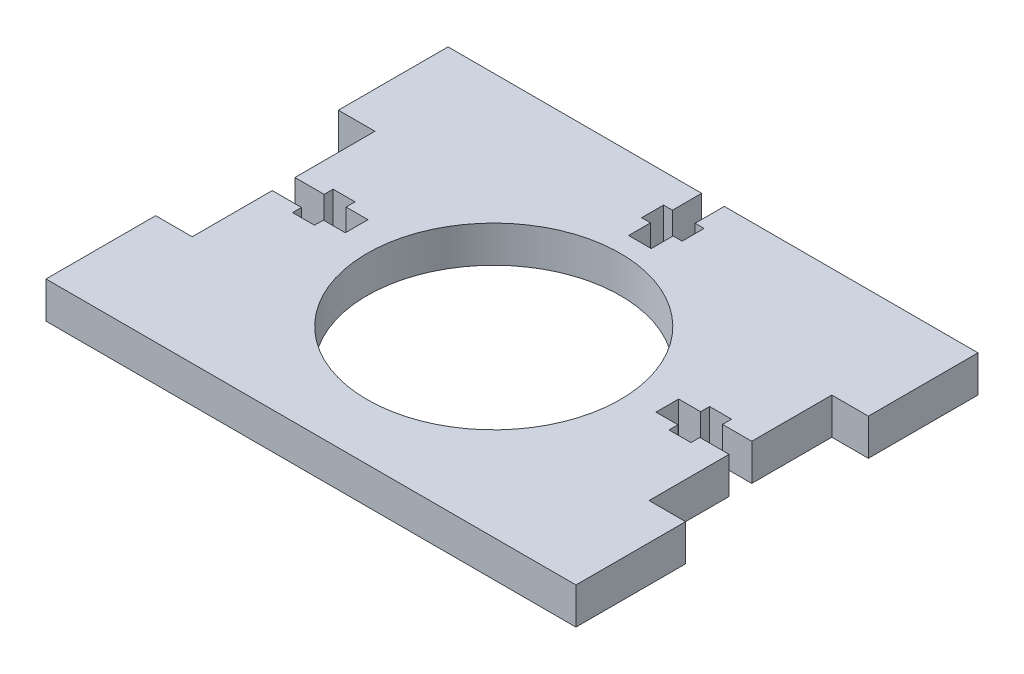
SolidWorks part; units mm, degrees
ref_plane "Plan de face" through (0, 0, 0) normal (0, 0, 1) x (1, 0, 0)
ref_plane "Plan de dessus" through (0, 0, 0) normal (0, 1, 0) x (1, 0, 0)
ref_plane "Plan de droite" through (0, 0, 0) normal (1, 0, 0) x (0, 0, -1)
ref_plane "Plan1" through (0, 5, 0) normal (0, 1, 0) x (1, 0, 0)
sketch "Esquisse1" plane through (0, 5, 0) normal (0, 1, 0) x (1, 0, 0)
  line L0 (31.25, -27.5) -> (31.25, 27.5)
  line L1 (31.25, 27.5) -> (5, 27.5)
  line L2 (5, 27.5) -> (5, -27.5)
  line L3 (5, -27.5) -> (31.25, -27.5)
extrude "Boss.-Extru.1" add sketch "Esquisse1" against normal blind 5
sketch "Esquisse2" plane through (31.25, 0, 0) normal (1, 0, 0) x (0, 0, -1)
  line L0 (27.5, 5) -> (27.5, 0)
  line L1 (27.5, 0) -> (15.45, 0)
  line L2 (15.45, 0) -> (12.5, 2.95)
  line L3 (12.5, 2.95) -> (12.5, 5)
  line L4 (12.5, 5) -> (27.5, 5)
extrude "Boss.-Extru.2" add sketch "Esquisse2" along normal blind 5
sketch "Esquisse3" plane through (31.25, 0, 0) normal (1, 0, 0) x (0, 0, -1)
  line L0 (-15.45, 0) -> (-27.5, 0)
  line L1 (-27.5, 0) -> (-27.5, 5)
  line L2 (-27.5, 5) -> (-12.5, 5)
  line L3 (-12.5, 5) -> (-12.5, 2.95)
  line L4 (-12.5, 2.95) -> (-15.45, 0)
extrude "Boss.-Extru.3" add sketch "Esquisse3" along normal blind 5
sketch "Esquisse4" plane through (0, 0, -27.5) normal (0, 0, -1) x (-1, 0, 0)
  line L0 (-5, 0) -> (-5, 2.95)
  line L1 (-5, 2.95) -> (-7.95, 0)
  line L2 (-7.95, 0) -> (-5, 0)
extrude "Enlèv. mat.-Extru.1" cut sketch "Esquisse4" against normal blind 5
sketch "Esquisse5" plane through (5, 0, 0) normal (-1, 0, 0) x (0, 0, 1)
  line L0 (-22.5, 5) -> (27.5, 5)
  line L1 (27.5, 5) -> (27.5, 0)
  line L2 (27.5, 0) -> (-22.5, 0)
  line L3 (-22.5, 0) -> (-22.5, 5)
extrude "Boss.-Extru.4" add sketch "Esquisse5" along normal blind 36.25
sketch "Esquisse6" plane through (-31.25, 0, 0) normal (-1, 0, 0) x (0, 0, 1)
  line L0 (27.5, 5) -> (27.5, 0)
  line L1 (27.5, 0) -> (15.45, 0)
  line L2 (15.45, 0) -> (12.5, 2.95)
  line L3 (12.5, 2.95) -> (12.5, 5)
  line L4 (12.5, 5) -> (27.5, 5)
extrude "Boss.-Extru.5" add sketch "Esquisse6" along normal blind 5
sketch "Esquisse7" plane through (-31.25, 0, 0) normal (-1, 0, 0) x (0, 0, 1)
  line L0 (-22.5, 5) -> (-12.5, 5)
  line L1 (-12.5, 5) -> (-12.5, 2.95)
  line L2 (-12.5, 2.95) -> (-15.45, 0)
  line L3 (-15.45, 0) -> (-22.5, 0)
  line L4 (-22.5, 0) -> (-22.5, 5)
extrude "Boss.-Extru.6" add sketch "Esquisse7" along normal blind 5
sketch "Esquisse8" plane through (0, 0, -22.5) normal (0, 0, -1) x (-1, 0, 0)
  line L0 (5, 2.95) -> (5, 5)
  line L1 (5, 5) -> (36.25, 5)
  line L2 (36.25, 5) -> (36.25, 0)
  line L3 (36.25, 0) -> (7.95, 0)
  line L4 (7.95, 0) -> (5, 2.95)
extrude "Boss.-Extru.7" add sketch "Esquisse8" along normal blind 5
hole_wizard "Dégagement M301" positions "Esquisse10" profile "Esquisse9" hole size "M30" standard "Ansi Metric"
sketch "Esquisse10" plane through (0, 5, 0) normal (0, 1, 0) x (1, 0, 0)
  point P0 (0, -2.5)
sketch "Esquisse9" plane through (0, 5, 2.5) normal (1, 0, 0) x (0, 0, 1)
  line L0 (0, 0) -> (0, 5)
  line L1 (0, 5) -> (17.325, 5)
  line L2 (17.325, 5) -> (17.325, 0)
  line L5 (17.325, 0) -> (0, 0)
  line L11 (0, -6.35) -> (0, 107.95) construction
  dimension "Diamètre du perçage jusqu'au prochain" = 34.65
  dimension "Profondeur du perçage jusqu'au prochain" = 5
fillet "Congé1" radius 1.6 6 edges at (-33.75, 2.95, 12.5) (-5, 2.95, -25) (-33.75, 2.95, -12.5) (33.75, 2.95, -12.5) (5, 2.95, -25) (33.75, 2.95, 12.5)
sketch "Esquisse11" plane through (0, 0, 0) normal (0, -1, 0) x (1, 0, 0)
  line L0 (36.25, -27.5) -> (7.95, -27.5) construction
  line L1 (10.0838, -27.5) -> (-9.9495, -27.5)
  line L2 (10.0838, -27.5) -> (10.0838, -21.3098)
  line L3 (10.0838, -21.3098) -> (-9.9495, -21.3098)
  line L4 (-9.9495, -27.5) -> (-9.9495, -21.3098)
  line L6 (-31.25, -15.45) -> (-36.25, -15.45)
  line L7 (-31.25, -15.45) -> (-31.25, -12.5)
  line L8 (-31.25, -12.5) -> (-36.25, -12.5)
  line L9 (-36.25, -15.45) -> (-36.25, -12.5)
  line L10 (-36.25, 12.5) -> (-31.25, 12.5)
  line L11 (-36.25, 12.5) -> (-36.25, 15.45)
  line L12 (-36.25, 15.45) -> (-31.25, 15.45)
  line L13 (-31.25, 12.5) -> (-31.25, 15.45)
  line L14 (31.25, 15.45) -> (36.25, 15.45)
  line L15 (31.25, 15.45) -> (31.25, 12.5)
  line L16 (31.25, 12.5) -> (36.25, 12.5)
  line L17 (36.25, 15.45) -> (36.25, 12.5)
  line L18 (36.25, -12.5) -> (31.25, -12.5)
  line L19 (36.25, -12.5) -> (36.25, -15.45)
  line L20 (36.25, -15.45) -> (31.25, -15.45)
  line L21 (31.25, -12.5) -> (31.25, -15.45)
extrude "Boss.-Extru.8" add sketch "Esquisse11" against normal blind 5
sketch "Esquisse12" plane through (0, 0, 0) normal (0, -1, 0) x (1, 0, 0)
  line L0 (36.25, -27.5) -> (-36.25, -27.5) construction
  line L1 (1.55, -27.5) -> (-1.55, -27.5)
  line L2 (1.55, -27.5) -> (1.55, -17.5)
  line L3 (1.55, -17.5) -> (-1.55, -17.5)
  line L4 (-1.55, -27.5) -> (-1.55, -17.5)
  line L6 (2.78, -23.5) -> (-2.77, -23.5)
  line L7 (2.78, -23.5) -> (2.78, -20.5)
  line L8 (2.78, -20.5) -> (-2.77, -20.5)
  line L9 (-2.77, -23.5) -> (-2.77, -20.5)
  line L18 (31.25, 12.5) -> (31.25, -12.5) construction
  line L19 (31.25, -1.55) -> (21.25, -1.55)
  line L20 (31.25, -1.55) -> (31.25, 1.55)
  line L21 (31.25, 1.55) -> (21.25, 1.55)
  line L22 (21.25, -1.55) -> (21.25, 1.55)
  line L23 (36.25, -12.5) -> (31.25, -12.5) construction
  line L24 (27.25, -2.78) -> (24.25, -2.78)
  line L25 (27.25, -2.78) -> (27.25, 2.77)
  line L26 (27.25, 2.77) -> (24.25, 2.77)
  line L27 (24.25, -2.78) -> (24.25, 2.77)
  line L28 (0, 0) -> (0, 12.6155) construction
  line L29 (-24.25, -2.78) -> (-24.25, 2.77)
  line L30 (-27.25, 2.77) -> (-24.25, 2.77)
  line L31 (-27.25, -2.78) -> (-27.25, 2.77)
  line L32 (-27.25, -2.78) -> (-24.25, -2.78)
  line L33 (-21.25, -1.55) -> (-21.25, 1.55)
  line L34 (-31.25, 1.55) -> (-21.25, 1.55)
  line L35 (-31.25, -1.55) -> (-31.25, 1.55)
  line L36 (-31.25, -1.55) -> (-21.25, -1.55)
  line M7 (31.25, -12.5) -> (31.25, 12.5)
  line M13 (-31.25, 12.5) -> (-31.25, -12.5)
  line M16 (-36.25, -27.5) -> (36.25, -27.5)
  dimension "D1" = 4
  dimension "D2" = 3
  dimension "D3" = 3
  dimension "D4" = 5.55
  dimension "D5" = 3.1
  dimension "D6" = 1.23
  dimension "D7" = 1.55
  dimension "D8" = 10
  dimension "D9" = 3
  dimension "D10" = 3
  dimension "D11" = 5.55
  dimension "D12" = 3.1
  dimension "D13" = 1.23
  dimension "D14" = 10.95
extrude "Enlèv. mat.-Extru.2" cut sketch "Esquisse12" against normal through all contours L2 L6 L4 M16 | L2 L8 L4 L6 | L7 L8 L2 L6 | L8 L2 L3 L4 | L9 L6 L4 L8 | L25 L19 L21 M7 | L27 L19 L25 L21 | L27 L24 L25 L19 | L19 L27 L21 L22 | L27 L21 L25 L26 | L29 L36 L33 L34 | L31 L36 L29 L34 | L36 L31 L32 L29 | L36 L31 L34 M13 | L31 L34 L29 L30
